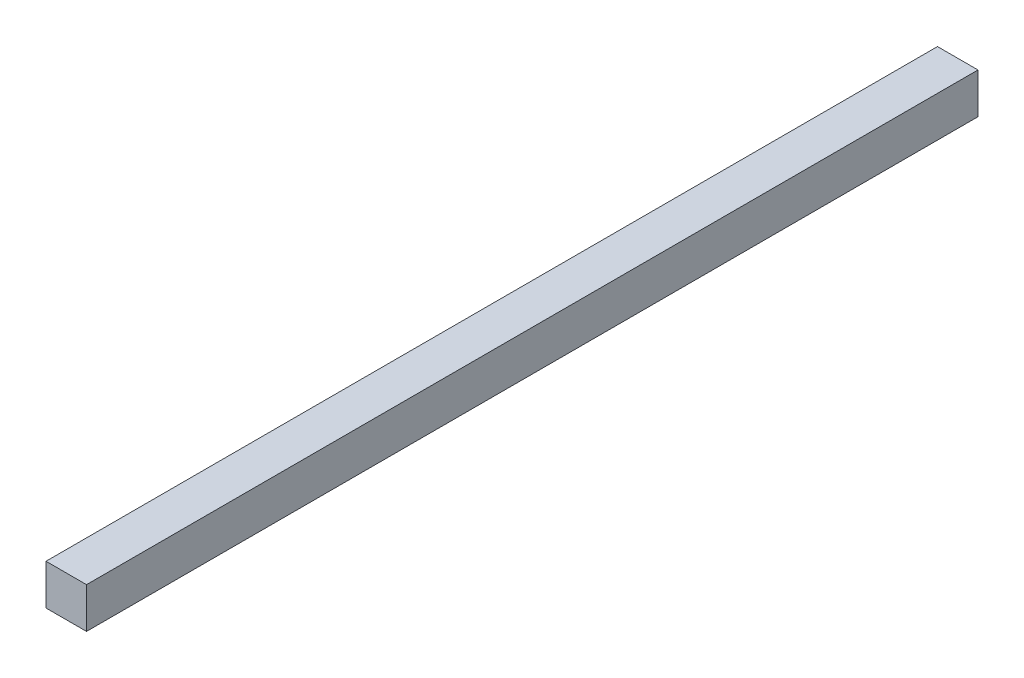
SolidWorks part; units mm, degrees
ref_plane "Front Plane" through (0, 0, 0) normal (0, 0, 1) x (1, 0, 0)
ref_plane "Top Plane" through (0, 0, 0) normal (0, 1, 0) x (1, 0, 0)
ref_plane "Right Plane" through (0, 0, 0) normal (1, 0, 0) x (0, 0, -1)
sketch "Sketch4" plane through (0, 0, 0) normal (0, 0, 1) x (1, 0, 0)
  line L1 (-12.7, -12.7) -> (12.7, -12.7)
  line L2 (-12.7, -12.7) -> (-12.7, 12.7)
  line L3 (-12.7, 12.7) -> (12.7, 12.7)
  line L4 (12.7, -12.7) -> (12.7, 12.7)
  line L5 (-12.7, -12.7) -> (12.7, 12.7) construction
  line L6 (-12.7, 12.7) -> (12.7, -12.7) construction
  point P0 (0, 0)
  dimension "D1" = 25.4
  dimension "D2" = 25.4
extrude "Boss-Extrude2" add sketch "Sketch4" along normal blind 558.8
